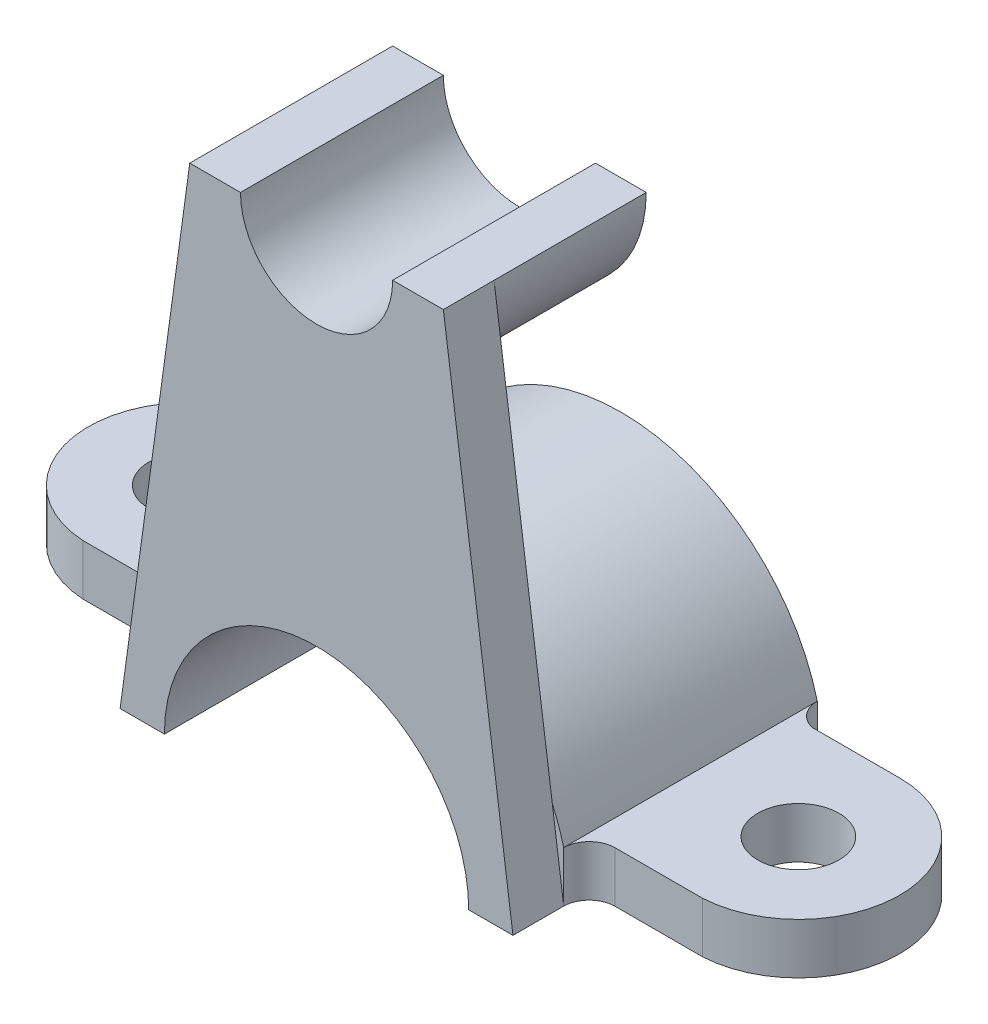
SolidWorks part; units mm, degrees
ref_plane "Front Plane" through (0, 0, 0) normal (0, 0, 1) x (1, 0, 0)
ref_plane "Top Plane" through (0, 0, 0) normal (0, 1, 0) x (1, 0, 0)
ref_plane "Right Plane" through (0, 0, 0) normal (1, 0, 0) x (0, 0, -1)
sketch "Sketch1" plane through (0, 0, 0) normal (0, 0, 1) x (1, 0, 0)
  line L0 (0, 104.0587) -> (0, -105.6324) construction
  line L1 (30, 0) -> (90, 0)
  line L2 (90, 0) -> (90, 10)
  line L3 (90, 10) -> (38.7298, 10)
  line L4 (-30, 0) -> (-90, 0)
  line L5 (-90, 0) -> (-90, 10)
  line L6 (-90, 10) -> (-38.7298, 10)
  arc A0 (30, 0) -> (-30, 0) centre (0, 0) ccw
  arc A1 (38.7298, 10) -> (-38.7298, 10) centre (0, 0) ccw
  dimension "D1" = 30
  dimension "D2" = 40
  dimension "D3" = 10
  dimension "D4" = 180
extrude "Boss-Extrude1" add sketch "Sketch1" along normal mid plane 50
sketch "Sketch2" plane through (0, 10, 0) normal (0, 1, 0) x (1, 0, 0)
  line L1 (-42.7599, 20) -> (-60, 20)
  line L2 (-61.0859, -19.9705) -> (-43.8458, -19.9705)
  line L4 (-38.7298, 25) -> (-90, 25) construction
  line L5 (-90, -25) -> (-90, 25) construction
  line L6 (-38.7298, -25) -> (-90, -25) construction
  line L7 (-38.7298, 25) -> (-90, 25)
  line L8 (-90, -25) -> (-90, 25)
  line L9 (-38.7298, -25) -> (-90, -25)
  circle A0 centre (-60, 0) radius 8
  arc A1 (-60, 20) -> (-61.0859, -19.9705) centre (-60, 0) ccw
  arc A2 (-43.8458, -19.9705) -> (-38.7298, -25) centre (-43.8458, -25.0872) cw
  arc A3 (-38.7298, 25) -> (-42.7599, 20) centre (-43.8466, 25) cw
  dimension "D1" = 60
  dimension "D2" = 16
  dimension "D3" = 20
extrude "Cut-Extrude1" cut sketch "Sketch2" against normal through all
mirror "Mirror1" about plane through (0, 0, 0) normal (1, 0, 0) of "Cut-Extrude1"
sketch "Sketch3" plane through (0, 0, 25) normal (0, 0, 1) x (1, 0, 0)
  line L0 (38.7298, 0) -> (-38.7298, 0)
  line L1 (-38.7298, 0) -> (-25, 100)
  line L2 (-25, 100) -> (25, 100)
  line L4 (38.7298, 0) -> (25, 100)
  dimension "D2" = 100
extrude "Boss-Extrude2" add sketch "Sketch3" along normal blind 10
sketch "Sketch5" plane through (0, 0, 25) normal (0, 0, -1) x (-1, 0, 0)
  line L0 (-30, 0) -> (30, 0)
  line L2 (-30, 0) -> (30, 0)
  line L3 (-30, 0) -> (30, 0)
  arc A1 (30, 0) -> (-30, 0) centre (0, 0) ccw
  arc A2 (30, 0) -> (-30, 0) centre (0, 0) ccw
  line M3 (-30, 0) -> (30, 0)
  arc M4 (30, 0) -> (-30, 0) centre (0, 0) ccw
  dimension "D1" = 0
extrude "Cut-Extrude2" cut sketch "Sketch5" against normal through all contours M4 M3
sketch "Sketch10" plane through (0, 0, 25) normal (0, 0, -1) x (-1, 0, 0)
  line L0 (-25, 100) -> (25, 100) construction
  line L4 (-25, 100) -> (25, 100)
  arc A0 (-25, 100) -> (25, 100) centre (0, 100) ccw
extrude "Boss-Extrude3" add sketch "Sketch10" along normal blind 30
sketch "Sketch11" plane through (0, 0, -5) normal (0, 0, -1) x (-1, 0, 0)
  line L0 (25, 100) -> (-25, 100) construction
  line L1 (15, 100) -> (-15, 100)
  arc A0 (15, 100) -> (-15, 100) centre (0, 100) cw
  dimension "D1" = 15
extrude "Cut-Extrude4" cut sketch "Sketch11" against normal through all
